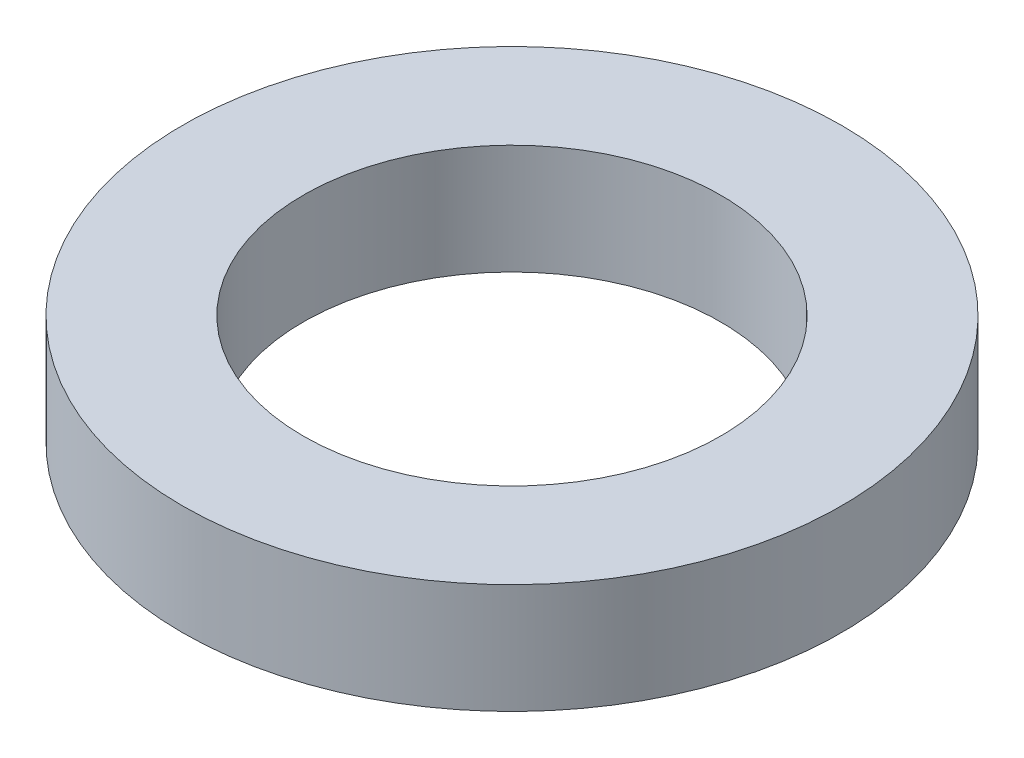
SolidWorks part; units mm, degrees
ref_plane "Front Plane" through (0, 0, 0) normal (0, 0, 1) x (1, 0, 0)
ref_plane "Top Plane" through (0, 0, 0) normal (0, 1, 0) x (1, 0, 0)
ref_plane "Right Plane" through (0, 0, 0) normal (1, 0, 0) x (0, 0, -1)
sketch "Sketch1" plane through (0, 0, 0) normal (0, 1, 0) x (1, 0, 0)
  circle A0 centre (0, 0) radius 3
  circle A1 centre (0, 0) radius 1.9
  dimension "D1" = 6
  dimension "D2" = 3.8
extrude "Boss-Extrude1" add sketch "Sketch1" along normal mid plane 1
